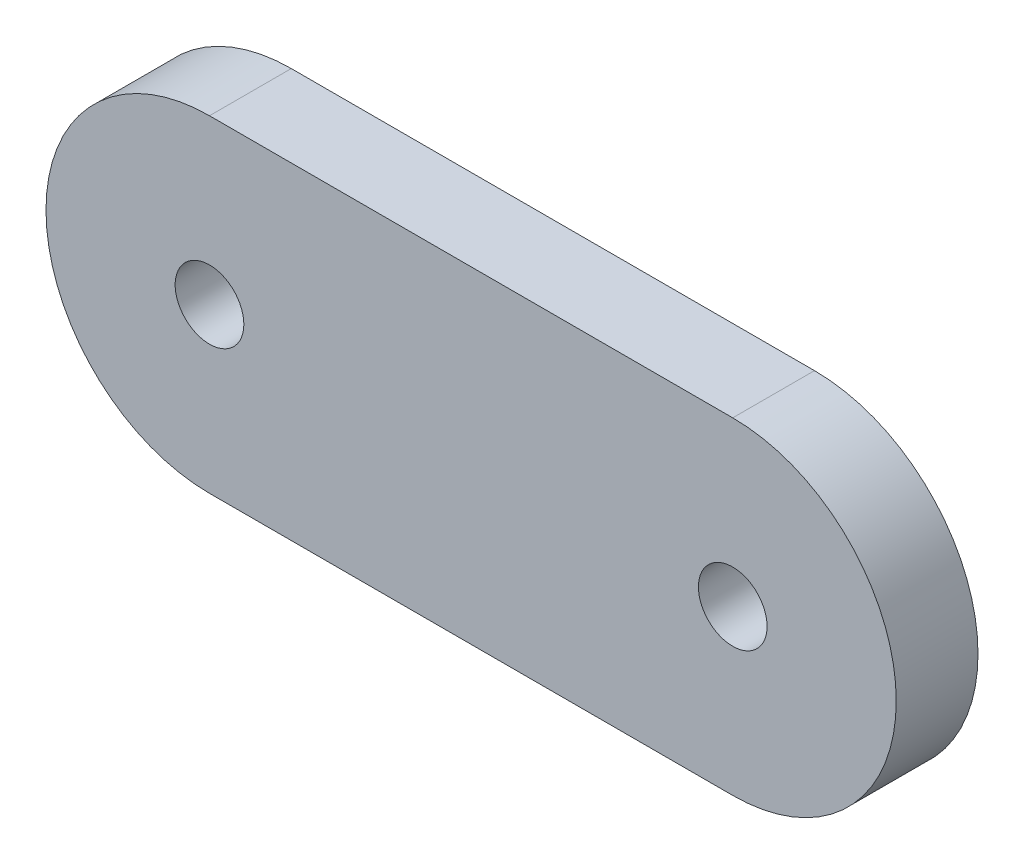
SolidWorks part; units mm, degrees
ref_plane "Front Plane" through (0, 0, 0) normal (0, 0, 1) x (1, 0, 0)
ref_plane "Top Plane" through (0, 0, 0) normal (0, 1, 0) x (1, 0, 0)
ref_plane "Right Plane" through (0, 0, 0) normal (1, 0, 0) x (0, 0, -1)
sketch "Sketch1" plane through (0, 0, 0) normal (0, 0, 1) x (1, 0, 0)
  line L0 (-43.7152, 0) -> (-11.7152, 0) construction
  line L1 (-43.7152, 10) -> (-11.7152, 10)
  line L2 (-43.7152, -10) -> (-11.7152, -10)
  arc A0 (-43.7152, 10) -> (-43.7152, -10) centre (-43.7152, 0) ccw
  arc A1 (-11.7152, -10) -> (-11.7152, 10) centre (-11.7152, 0) ccw
  circle A2 centre (-43.7152, 0) radius 2.1
  circle A3 centre (-11.7152, 0) radius 2.1
  point P3 (-27.7152, 0)
  dimension "D2" = 10
  dimension "D3" = 16
  dimension "D4" = 4.2
  dimension "D5" = 4.2
  dimension "D1" = 32
extrude "Boss-Extrude1" add sketch "Sketch1" along normal blind 5
